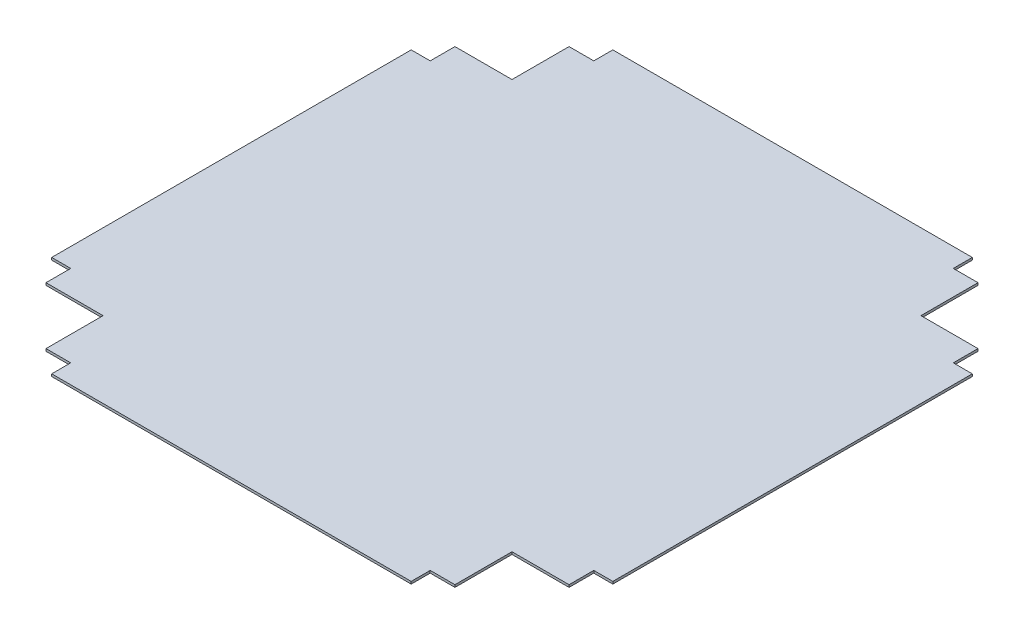
SolidWorks part; units mm, degrees
ref_plane "Front Plane" through (0, 0, 0) normal (0, 0, 1) x (1, 0, 0)
ref_plane "Top Plane" through (0, 0, 0) normal (0, 1, 0) x (1, 0, 0)
ref_plane "Right Plane" through (0, 0, 0) normal (1, 0, 0) x (0, 0, -1)
sketch "Sketch1" plane through (0, 0, 0) normal (0, 1, 0) x (1, 0, 0)
  line L0 (0, 0) -> (50000, 0) construction
  line L1 (-374.65, 374.65) -> (374.65, 374.65)
  line L2 (-374.65, 374.65) -> (-374.65, -374.65)
  line L3 (-374.65, -374.65) -> (374.65, -374.65)
  line L4 (374.65, 374.65) -> (374.65, -374.65)
  line L5 (-374.65, 374.65) -> (-273.05, 374.65)
  line L6 (-374.65, 374.65) -> (-374.65, 273.05)
  line L7 (-374.65, 273.05) -> (-273.05, 273.05)
  line L8 (-273.05, 374.65) -> (-273.05, 273.05)
  line L9 (374.65, 374.65) -> (273.05, 374.65)
  line L10 (374.65, 374.65) -> (374.65, 273.05)
  line L11 (374.65, 273.05) -> (273.05, 273.05)
  line L12 (273.05, 374.65) -> (273.05, 273.05)
  line L13 (374.65, -374.65) -> (273.05, -374.65)
  line L14 (374.65, -374.65) -> (374.65, -273.05)
  line L15 (374.65, -273.05) -> (273.05, -273.05)
  line L16 (273.05, -374.65) -> (273.05, -273.05)
  line L17 (-374.65, -374.65) -> (-273.05, -374.65)
  line L18 (-374.65, -374.65) -> (-374.65, -273.05)
  line L19 (-374.65, -273.05) -> (-273.05, -273.05)
  line L20 (-273.05, -374.65) -> (-273.05, -273.05)
  line L21 (-273.05, -349.25) -> (-240.03, -349.25)
  line L22 (-273.05, -349.25) -> (-273.05, -374.65)
  line L23 (-273.05, -374.65) -> (-240.03, -374.65)
  line L24 (-240.03, -349.25) -> (-240.03, -374.65)
  line L25 (273.05, -349.25) -> (240.03, -349.25)
  line L26 (273.05, -349.25) -> (273.05, -374.65)
  line L27 (273.05, -374.65) -> (240.03, -374.65)
  line L28 (240.03, -349.25) -> (240.03, -374.65)
  line L29 (-374.65, -273.05) -> (-349.25, -273.05)
  line L30 (-374.65, -273.05) -> (-374.65, -240.03)
  line L31 (-374.65, -240.03) -> (-349.25, -240.03)
  line L32 (-349.25, -273.05) -> (-349.25, -240.03)
  line L33 (374.65, -273.05) -> (349.25, -273.05)
  line L34 (374.65, -273.05) -> (374.65, -240.03)
  line L35 (374.65, -240.03) -> (349.25, -240.03)
  line L36 (349.25, -273.05) -> (349.25, -240.03)
  line L37 (374.65, 240.03) -> (349.25, 240.03)
  line L38 (349.25, 273.05) -> (349.25, 240.03)
  line L39 (374.65, 273.05) -> (349.25, 273.05)
  line L40 (374.65, 273.05) -> (374.65, 240.03)
  line L41 (273.05, 374.65) -> (240.03, 374.65)
  line L42 (240.03, 349.25) -> (240.03, 374.65)
  line L43 (273.05, 349.25) -> (240.03, 349.25)
  line L44 (273.05, 349.25) -> (273.05, 374.65)
  line L45 (-273.05, 374.65) -> (-240.03, 374.65)
  line L46 (-240.03, 349.25) -> (-240.03, 374.65)
  line L47 (-273.05, 349.25) -> (-240.03, 349.25)
  line L48 (-273.05, 349.25) -> (-273.05, 374.65)
  line L49 (-374.65, 240.03) -> (-349.25, 240.03)
  line L50 (-349.25, 273.05) -> (-349.25, 240.03)
  line L51 (-374.65, 273.05) -> (-349.25, 273.05)
  line L52 (-374.65, 273.05) -> (-374.65, 240.03)
  point P4 (0, 374.65)
  point P6 (-374.65, 0)
  dimension "D1" = 749.3
  dimension "D2" = 749.3
  dimension "D3" = 101.6
  dimension "D4" = 25.4
  dimension "D5" = 33.02
extrude "Boss-Extrude1" add sketch "Sketch1" along normal blind 3.175 contours L0 L2 L31 L32 L19 L20 L21 L24 L3 L28 L25 L16 L15 L36 L35 L4 | L2 L0 L4 L37 L38 L11 L12 L43 L42 L1 L46 L47 L8 L7 L50 L49
